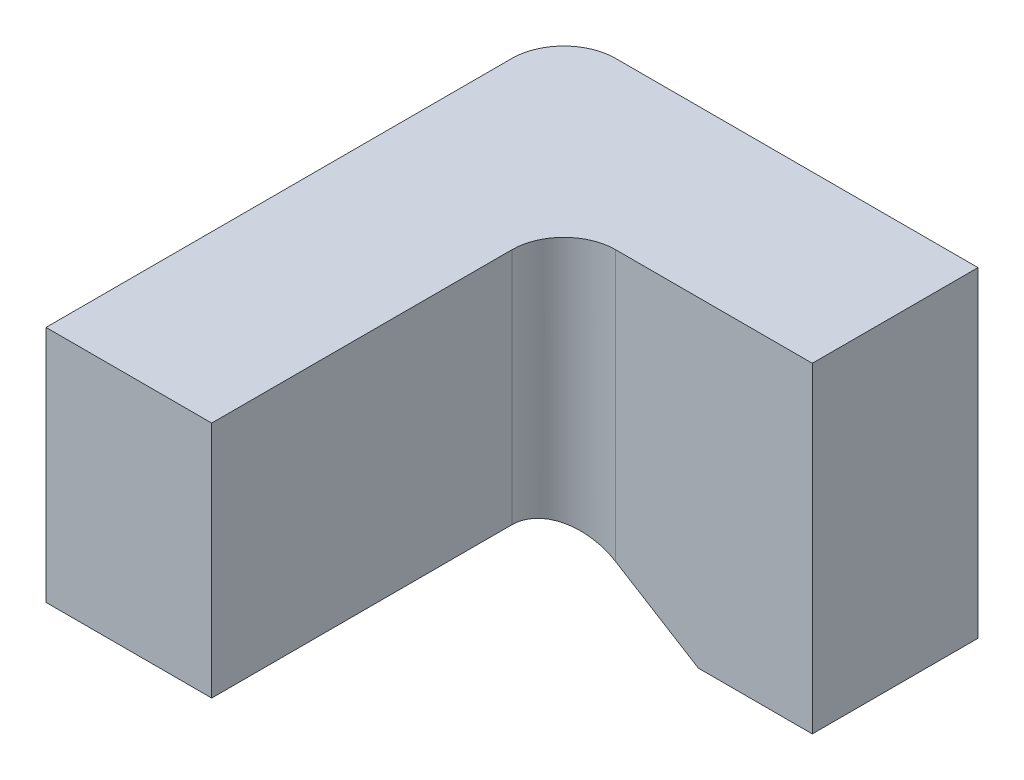
SolidWorks part; units mm, degrees
ref_plane "前视基准面" through (0, 0, 0) normal (0, 0, 1) x (1, 0, 0)
ref_plane "上视基准面" through (0, 0, 0) normal (0, 1, 0) x (1, 0, 0)
ref_plane "右视基准面" through (0, 0, 0) normal (1, 0, 0) x (0, 0, -1)
sketch "草图1" plane through (0, 0, 0) normal (0, 0, 1) x (1, 0, 0)
  line L0 (0, 0) -> (0.4, 0)
  line L1 (0.4, 0) -> (0.4, -0.31)
  line L2 (0.4, -0.31) -> (0.29, -0.31)
  line L3 (0.29, -0.31) -> (0.16, -0.23)
  line L4 (0.16, -0.23) -> (0, -0.23)
  line L5 (0, -0.23) -> (0, 0)
  dimension "D1" = 0.23
  dimension "D2" = 0.31
  dimension "D3" = 0.4
  dimension "D4" = 0.11
  dimension "D5" = 0.16
extrude "凸台-拉伸1" add sketch "草图1" along normal blind 0.16
sketch "草图2" plane through (0, 0, 0.16) normal (0, 0, 1) x (1, 0, 0)
  line L1 (0, 0) -> (0.16, 0)
  line L2 (0, 0) -> (0, -0.23)
  line L3 (0, -0.23) -> (0.16, -0.23)
  line L4 (0.16, 0) -> (0.16, -0.23)
extrude "凸台-拉伸2" add sketch "草图2" along normal blind 0.34
fillet "圆角1" radius 0.05 1 edges at (0, -0.115, 0)
fillet "圆角2" radius 0.05 1 edges at (0.16, -0.115, 0.16)
